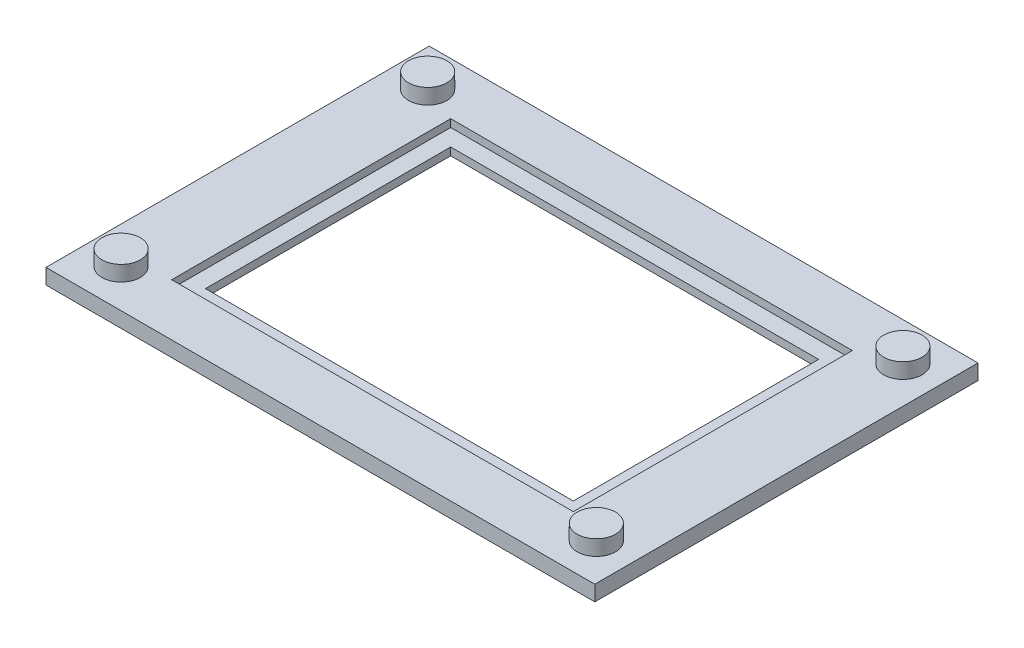
SolidWorks part; units mm, degrees
ref_plane "Front Plane" through (0, 0, 0) normal (0, 0, 1) x (1, 0, 0)
ref_plane "Top Plane" through (0, 0, 0) normal (0, 1, 0) x (1, 0, 0)
ref_plane "Right Plane" through (0, 0, 0) normal (1, 0, 0) x (0, 0, -1)
sketch "Sketch1" plane through (0, 0, 0) normal (0, 1, 0) x (1, 0, 0)
  line L1 (-17.9, -12.5) -> (17.9, -12.5)
  line L2 (-17.9, -12.5) -> (-17.9, 12.5)
  line L3 (-17.9, 12.5) -> (17.9, 12.5)
  line L4 (17.9, -12.5) -> (17.9, 12.5)
  line L5 (-17.9, -12.5) -> (17.9, 12.5) construction
  line L6 (-17.9, 12.5) -> (17.9, -12.5) construction
  line L7 (-12, -8) -> (12, -8)
  line L8 (-12, -8) -> (-12, 8)
  line L9 (-12, 8) -> (12, 8)
  line L10 (12, -8) -> (12, 8)
  line L11 (-12, -8) -> (12, 8) construction
  line L12 (-12, 8) -> (12, -8) construction
  point P0 (0, 0)
  point P6 (0, 0)
  dimension "D1" = 25
  dimension "D2" = 35.8
  dimension "D3" = 16
  dimension "D4" = 24
extrude "Boss-Extrude1" add sketch "Sketch1" along normal blind 1
sketch "Sketch2" plane through (0, 1, 0) normal (0, 1, 0) x (1, 0, 0)
  line L1 (-13.1, -9.1) -> (13.1, -9.1)
  line L2 (-13.1, -9.1) -> (-13.1, 9.1)
  line L3 (-13.1, 9.1) -> (13.1, 9.1)
  line L4 (13.1, -9.1) -> (13.1, 9.1)
  line L5 (-13.1, -9.1) -> (13.1, 9.1) construction
  line L6 (-13.1, 9.1) -> (13.1, -9.1) construction
  point P0 (0, 0)
  dimension "D1" = 18.2
  dimension "D2" = 26.2
extrude "Cut-Extrude1" cut sketch "Sketch2" against normal blind 0.5
sketch "Sketch4" plane through (0, 1, 0) normal (0, 1, 0) x (1, 0, 0)
  line L1 (-15.5, -10) -> (15.5, -10) construction
  line L2 (-15.5, -10) -> (-15.5, 10) construction
  line L3 (-15.5, 10) -> (15.5, 10) construction
  line L4 (15.5, -10) -> (15.5, 10) construction
  line L5 (-15.5, -10) -> (15.5, 10) construction
  line L6 (-15.5, 10) -> (15.5, -10) construction
  circle A0 centre (-15.5, 10) radius 1.25
  circle A1 centre (-15.5, -10) radius 1.25
  circle A2 centre (15.5, -10) radius 1.25
  circle A3 centre (15.5, 10) radius 1.25
  point P0 (0, 0)
  dimension "D1" = 2.5
  dimension "D2" = 31
  dimension "D3" = 20
extrude "Boss-Extrude2" add sketch "Sketch4" along normal blind 1
